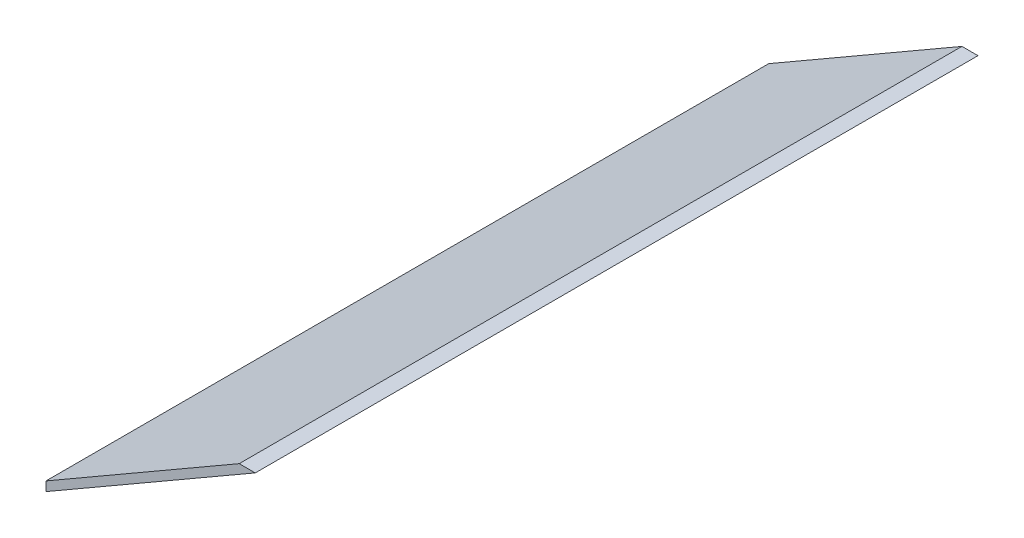
SolidWorks part; units mm, degrees
ref_plane "Ebene vorne" through (0, 0, 0) normal (0, 0, 1) x (1, 0, 0)
ref_plane "Ebene oben" through (0, 0, 0) normal (0, 1, 0) x (1, 0, 0)
ref_plane "Ebene rechts" through (0, 0, 0) normal (1, 0, 0) x (0, 0, -1)
sketch "Skizze1" plane through (0, 0, 0) normal (0, 0, 1) x (1, 0, 0)
  line L0 (227.8045, 257.7313) -> (217.8045, 257.7313)
  line L1 (97.5, 188.2735) -> (97.5, 182.5)
  line L30 (97.5, 188.2735) -> (217.8045, 257.7313)
  line L31 (97.5, 182.5) -> (227.8045, 257.7313)
extrude "Aufsatz-Linear austragen1" add sketch "Skizze1" along normal blind 450
